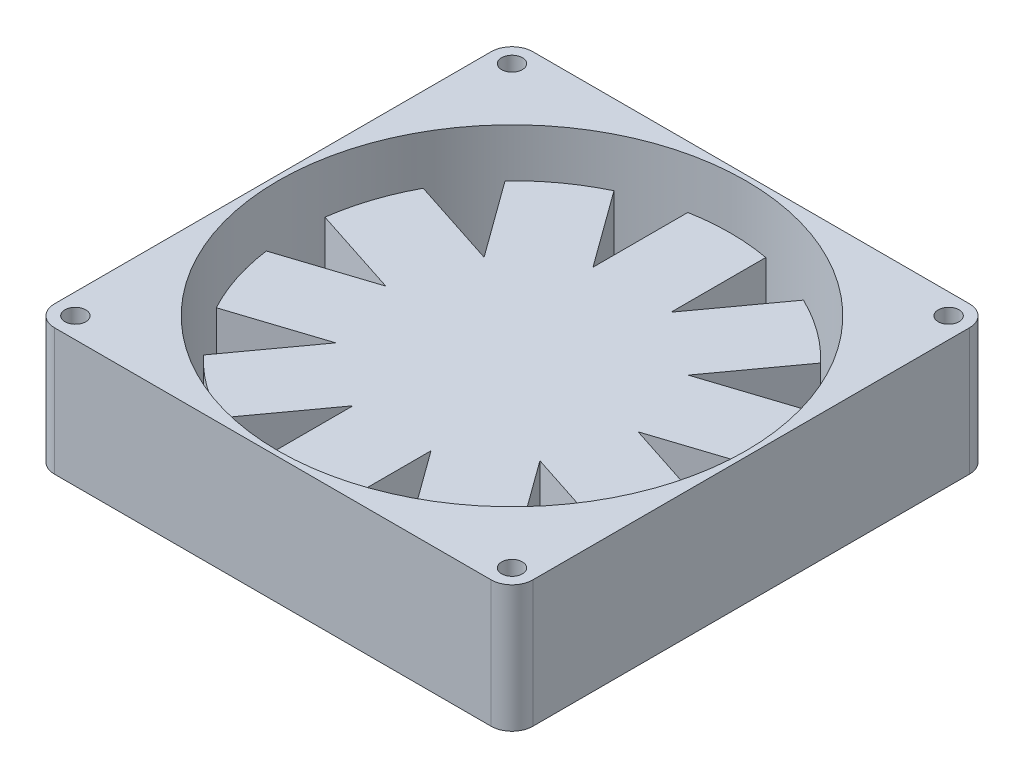
SolidWorks part; units mm, degrees
ref_plane "Plano frontal" through (0, 0, 0) normal (0, 0, 1) x (1, 0, 0)
ref_plane "Plano superior" through (0, 0, 0) normal (0, 1, 0) x (1, 0, 0)
ref_plane "Plano direito" through (0, 0, 0) normal (1, 0, 0) x (0, 0, -1)
sketch "Esboço1" plane through (0, 0, 0) normal (0, 1, 0) x (1, 0, 0)
  line L1 (46, -46) -> (-46, -46)
  line L2 (46, -46) -> (46, 46)
  line L3 (46, 46) -> (-46, 46)
  line L4 (-46, -46) -> (-46, 46)
  line L5 (46, -46) -> (-46, 46) construction
  line L6 (46, 46) -> (-46, -46) construction
  point P0 (0, 0)
  dimension "D1" = 92
  dimension "D2" = 92
extrude "Ressalto-extrusão1" add sketch "Esboço1" along normal blind 24.4
sketch "Esboço2" plane through (0, 24.4, 0) normal (0, 1, 0) x (1, 0, 0)
  line L0 (46, -46) -> (46, 46) construction
  line L1 (46, 46) -> (-46, 46) construction
  line L2 (0, -54.2609) -> (0, 63.9482) construction
  line L3 (-64.0623, 0) -> (63.4936, 0) construction
  circle A0 centre (42, 42) radius 2
  circle A1 centre (-42, 42) radius 2
  circle A2 centre (42, -42) radius 2
  circle A3 centre (-42, -42) radius 2
  dimension "D1" = 4
  dimension "D2" = 4
  dimension "D3" = 4
extrude "Corte-extrusão1" cut sketch "Esboço2" against normal through all
fillet "Filete1" radius 4 4 edges at (46, 12.2, 46) (-46, 12.2, 46) (46, 12.2, -46) (-46, 12.2, -46)
sketch "Esboço3" plane through (0, 24.4, 0) normal (0, 1, 0) x (1, 0, 0)
  circle A0 centre (0, 0) radius 45
  dimension "D1" = 90
extrude "Corte-extrusão3" cut sketch "Esboço3" against normal through all
ref_plane "Plano1" through (0, 17.2, 0) normal (0, 1, 0) x (1, 0, 0)
sketch "Esboço4" plane through (0, 17.2, 0) normal (0, 1, 0) x (1, 0, 0)
  line L1 (0, -55.1534) -> (0, -42) construction
  line L2 (-71.1999, 0) -> (-24.2705, 0) construction
  line L3 (-7.5, 41.3249) -> (-7.5, 23.0826)
  line L4 (7.5, 41.3249) -> (7.5, 23.0826)
  line L5 (18.2226, 37.841) -> (7.5, 23.0826)
  line L6 (30.3578, 29.0242) -> (19.6353, 14.2658)
  line L7 (36.9847, 19.903) -> (19.6353, 14.2658)
  line L8 (41.62, 5.6372) -> (24.2705, 0)
  line L9 (41.62, -5.6372) -> (24.2705, 0)
  line L10 (36.9847, -19.903) -> (19.6353, -14.2658)
  line L11 (30.3578, -29.0242) -> (19.6353, -14.2658)
  line L12 (18.2226, -37.841) -> (7.5, -23.0826)
  line L13 (7.5, -41.3249) -> (7.5, -23.0826)
  line L14 (-7.5, -41.3249) -> (-7.5, -23.0826)
  line L15 (-18.2226, -37.841) -> (-7.5, -23.0826)
  line L16 (-30.3578, -29.0242) -> (-19.6353, -14.2658)
  line L17 (-36.9847, -19.903) -> (-19.6353, -14.2658)
  line L18 (-41.62, -5.6372) -> (-24.2705, 0)
  line L19 (-41.62, 5.6372) -> (-24.2705, 0)
  line L20 (-36.9847, 19.903) -> (-19.6353, 14.2658)
  line L21 (-30.3578, 29.0242) -> (-19.6353, 14.2658)
  line L22 (-18.2226, 37.841) -> (-7.5, 23.0826)
  line L27 (0, 42) -> (0, 53.8781) construction
  line L33 (24.2705, 0) -> (56.1098, 0) construction
  line L40 (0, -42) -> (0, -55.1534) construction
  arc A1 (-7.5, 41.3249) -> (7.5, 41.3249) centre (0, 0) cw
  arc A2 (18.2226, 37.841) -> (30.3578, 29.0242) centre (0, 0) cw
  arc A3 (36.9847, 19.903) -> (41.62, 5.6372) centre (0, 0) cw
  arc A4 (41.62, -5.6372) -> (36.9847, -19.903) centre (0, 0) cw
  arc A5 (30.3578, -29.0242) -> (18.2226, -37.841) centre (0, 0) cw
  arc A6 (7.5, -41.3249) -> (-7.5, -41.3249) centre (0, 0) cw
  arc A7 (-18.2226, -37.841) -> (-30.3578, -29.0242) centre (0, 0) cw
  arc A8 (-36.9847, -19.903) -> (-41.62, -5.6372) centre (0, 0) cw
  arc A9 (-41.62, 5.6372) -> (-36.9847, 19.903) centre (0, 0) cw
  arc A10 (-30.3578, 29.0242) -> (-18.2226, 37.841) centre (0, 0) cw
  point P9 (0, 42)
  dimension "D1" = 42
  dimension "D2" = 15
  dimension "D3" = 10
extrude "Ressalto-extrusão2" add sketch "Esboço4" against normal blind 15 separate body
